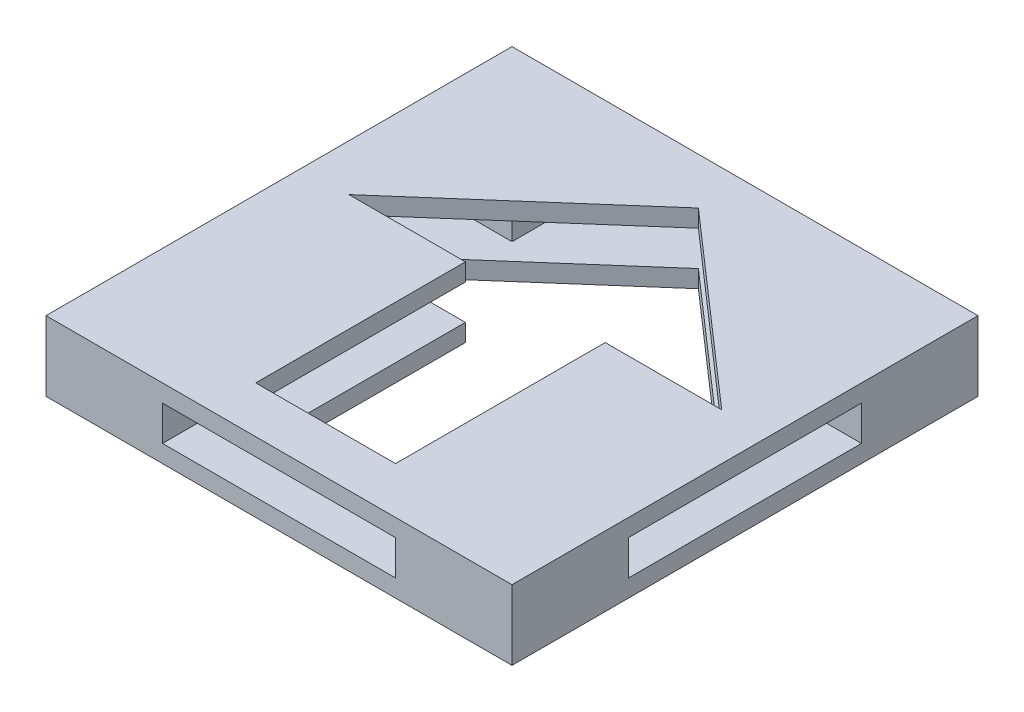
SolidWorks part; units mm, degrees
ref_plane "Front Plane" through (0, 0, 0) normal (0, 0, 1) x (1, 0, 0)
ref_plane "Top Plane" through (0, 0, 0) normal (0, 1, 0) x (1, 0, 0)
ref_plane "Right Plane" through (0, 0, 0) normal (1, 0, 0) x (0, 0, -1)
sketch "Sketch1" plane through (0, 0, 0) normal (0, 1, 0) x (1, 0, 0)
  line L0 (-8, 8) -> (-8, 1) construction
  line L1 (-10, 10) -> (10, 10)
  line L2 (-10, 10) -> (-10, -10)
  line L3 (-10, -10) -> (10, -10)
  line L4 (10, 10) -> (10, -10)
  line L5 (8, -8) -> (-8, -8) construction
  line L6 (8, -8) -> (8, 8) construction
  line L7 (8, 8) -> (-8, 8) construction
  line L8 (-8, -8) -> (-8, 8) construction
  line L9 (-8, 1) -> (-3, 1)
  line L10 (8, 1) -> (0, 8)
  line L11 (0, 8) -> (-8, 1)
  line L12 (3, 1) -> (8, 1)
  line L13 (3, -8) -> (-3, -8)
  line L14 (3, -8) -> (3, 1)
  line L16 (-3, -8) -> (-3, 1)
  point P0 (0, 0)
  point P4 (0, 0)
  dimension "D1" = 20
  dimension "D2" = 20
  dimension "D3" = 16
  dimension "D4" = 16
  dimension "D5" = 7
  dimension "D6" = 6
  dimension "D7" = 5
extrude "Boss-Extrude1" add sketch "Sketch1" along normal blind 3
sketch "Sketch2" plane through (0, 0, 10) normal (0, 0, 1) x (1, 0, 0)
  line L0 (-10, 3) -> (-10, 0) construction
  line L1 (5, 0.75) -> (-5, 0.75)
  line L2 (5, 0.75) -> (5, 2.25)
  line L3 (5, 2.25) -> (-5, 2.25)
  line L4 (-5, 0.75) -> (-5, 2.25)
  line L5 (0, 2.25) -> (0, 0.75) construction
  line L6 (5, 1.5) -> (-5, 1.5) construction
  line L8 (-10, 0) -> (10, 0) construction
  point P0 (0, 1.5)
  dimension "D1" = 10
  dimension "D2" = 5
  dimension "D3" = 1.5
  dimension "D4" = 0.75
extrude "Cut-Extrude1" cut sketch "Sketch2" against normal through all
sketch "Sketch3" plane through (10, 0, 0) normal (1, 0, 0) x (0, 0, -1)
  line L0 (-10, 3) -> (-10, 0) construction
  line L1 (5, 0.75) -> (-5, 0.75)
  line L2 (5, 0.75) -> (5, 2.25)
  line L3 (5, 2.25) -> (-5, 2.25)
  line L4 (-5, 0.75) -> (-5, 2.25)
  line L5 (0, 2.25) -> (0, 0.75) construction
  line L6 (5, 1.5) -> (-5, 1.5) construction
  line L7 (-10, 0) -> (10, 0) construction
  point P0 (0, 1.5)
  dimension "D1" = 10
  dimension "D2" = 5
  dimension "D3" = 0.75
  dimension "D4" = 1.5
extrude "Cut-Extrude2" cut sketch "Sketch3" against normal through all
